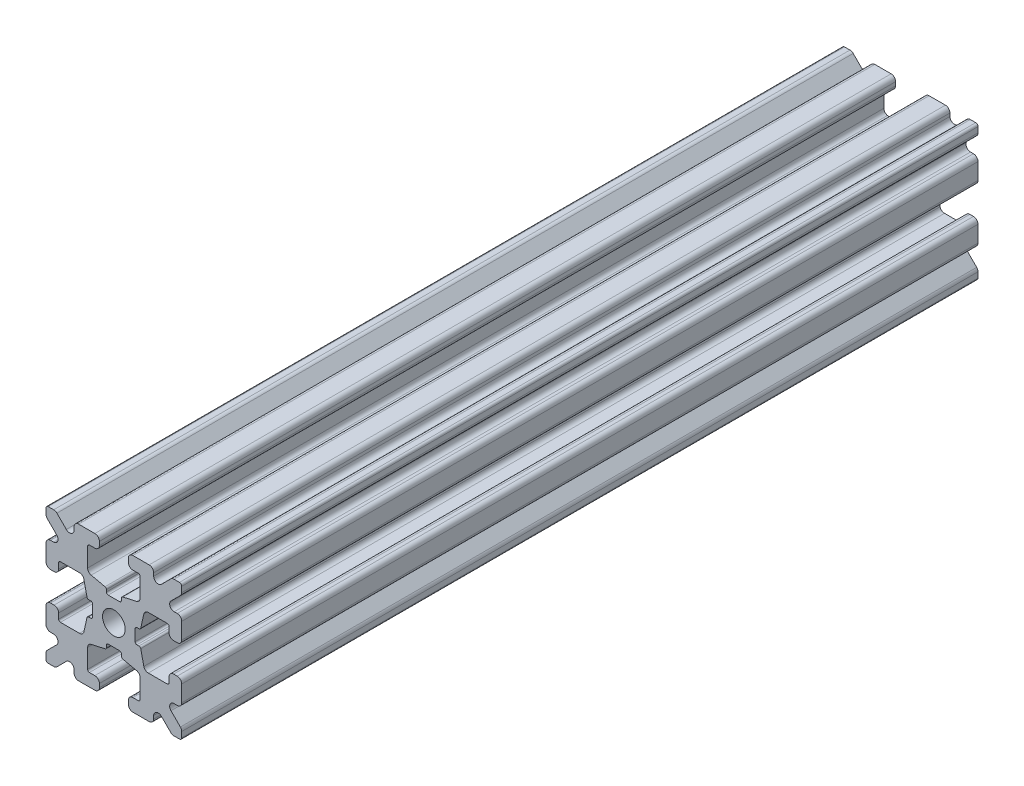
SolidWorks part; units mm, degrees
ref_plane "Front Plane" through (0, 0, 0) normal (0, 0, 1) x (1, 0, 0)
ref_plane "Top Plane" through (0, 0, 0) normal (0, 1, 0) x (1, 0, 0)
ref_plane "Right Plane" through (0, 0, 0) normal (1, 0, 0) x (0, 0, -1)
sketch "Sketch1" plane through (0, 0, 0) normal (0, 0, 1) x (1, 0, 0)
  line L1 (-7.5, -7.5) -> (7.5, -7.5)
  line L2 (-7.5, -7.5) -> (-7.5, 7.5)
  line L3 (-7.5, 7.5) -> (7.5, 7.5)
  line L4 (7.5, -7.5) -> (7.5, 7.5)
  line L5 (-7.5, -7.5) -> (7.5, 7.5) construction
  line L6 (-7.5, 7.5) -> (7.5, -7.5) construction
  circle A0 centre (0, 0) radius 1.25
  point P0 (0, 0)
  dimension "D2" = 2.5
  dimension "D1" = 15
extrude "Boss-Extrude1" add sketch "Sketch1" along normal mid plane 88
fillet "Fillet1" radius 0.25 4 edges at (7.5, -7.5, 0) (-7.5, -7.5, 0) (7.5, 7.5, 0) (-7.5, 7.5, 0)
sketch "Sketch2" plane through (0, 0, 44) normal (0, 0, 1) x (1, 0, 0)
  line L0 (-7.5, 7.25) -> (-7.5, -7.25) construction
  line L1 (-7.5, 1.6) -> (-6.1, 1.6)
  line L2 (-7.5, 1.6) -> (-7.5, -1.6)
  line L3 (-7.5, -1.6) -> (-6.1, -1.6)
  line L4 (-6.1, 1.6) -> (-6.1, 2.9)
  line L5 (0, 0) -> (-12.1036, 0) construction
  line L6 (-6.1, -2.9) -> (-3.4, -2.9)
  line L7 (0, 0) -> (-7.25, 7.25) construction
  line L8 (-6.1, 2.9) -> (-3.4, 2.9)
  line L9 (-3.4, -2.9) -> (-3.4, 2.9)
  line L10 (55, 0) -> (-55, 0) construction
  line L11 (-6.1, -2.9) -> (-6.1, -1.6)
  line L12 (2.9, 6.1) -> (1.6, 6.1)
  line L13 (2.9, 3.4) -> (-2.9, 3.4)
  line L14 (-2.9, 6.1) -> (-2.9, 3.4)
  line L15 (2.9, 6.1) -> (2.9, 3.4)
  line L16 (-1.6, 6.1) -> (-2.9, 6.1)
  line L17 (1.6, 7.5) -> (1.6, 6.1)
  line L18 (-1.6, 7.5) -> (1.6, 7.5)
  line L19 (-1.6, 7.5) -> (-1.6, 6.1)
  line L20 (-1.6, -7.5) -> (-1.6, -6.1)
  line L21 (-1.6, -7.5) -> (1.6, -7.5)
  line L22 (1.6, -7.5) -> (1.6, -6.1)
  line L23 (-1.6, -6.1) -> (-2.9, -6.1)
  line L24 (2.9, -6.1) -> (2.9, -3.4)
  line L25 (-2.9, -6.1) -> (-2.9, -3.4)
  line L26 (2.9, -3.4) -> (-2.9, -3.4)
  line L27 (2.9, -6.1) -> (1.6, -6.1)
  line L28 (6.1, -2.9) -> (6.1, -1.6)
  line L29 (3.4, -2.9) -> (3.4, 2.9)
  line L30 (6.1, 2.9) -> (3.4, 2.9)
  line L31 (6.1, -2.9) -> (3.4, -2.9)
  line L32 (6.1, 1.6) -> (6.1, 2.9)
  line L33 (7.5, -1.6) -> (6.1, -1.6)
  line L34 (7.5, 1.6) -> (7.5, -1.6)
  line L35 (7.5, 1.6) -> (6.1, 1.6)
  dimension "D1" = 3.2
  dimension "D2" = 5.8
  dimension "D3" = 1.4
  dimension "D4" = 2.7
extrude "Cut-Extrude1" cut sketch "Sketch2" against normal through all
sketch "Sketch4" plane through (0, 0, 44) normal (0, 0, 1) x (1, 0, 0)
  line L0 (-3.4, 2.9) -> (-2.75, 0)
  line L1 (55, 0) -> (-55, 0) construction
  line L2 (-2.75, 0) -> (-3.4, -2.9)
  line L3 (-3.4, -2.9) -> (-3.4, 2.9) construction
  line L4 (-3.4, 2.9) -> (-3.4, -2.9)
  line L5 (-2.9, 3.4) -> (0, 2.75)
  line L6 (0, 2.75) -> (2.9, 3.4)
  line L7 (2.9, 3.4) -> (-2.9, 3.4)
  line L8 (3.4, 2.9) -> (2.75, 0)
  line L9 (2.75, 0) -> (3.4, -2.9)
  line L10 (3.4, -2.9) -> (3.4, 2.9)
  line L11 (-2.9, -3.4) -> (0, -2.75)
  line L12 (0, -2.75) -> (2.9, -3.4)
  line L13 (2.9, -3.4) -> (-2.9, -3.4)
  circle A2 centre (0, 0) radius 2.75
  circle A3 centre (0, 0) radius 2.75 construction
  dimension "D1" = 1.5
extrude "Cut-Extrude3" cut sketch "Sketch4" against normal through all
fillet "Fillet3" radius 0.5 16 edges at (-6.1, -1.6, 0) (-7.5, -1.6, 0) (-6.1, 1.6, 0) (-7.5, 1.6, 0) (-1.6, -7.5, 0) (-1.6, -6.1, 0) (1.6, -7.5, 0) (1.6, -6.1, 0) (6.1, -1.6, 0) (7.5, -1.6, 0) (7.5, 1.6, 0) (6.1, 1.6, 0) (1.6, 7.5, 0) (1.6, 6.1, 0) (-1.6, 7.5, 0) (-1.6, 6.1, 0)
fillet "Fillet4" radius 0.5 8 edges at (-3.4, 2.9, 0) (-3.4, -2.9, 0) (2.9, -3.4, 0) (-2.9, -3.4, 0) (3.4, -2.9, 0) (3.4, 2.9, 0) (-2.9, 3.4, 0) (2.9, 3.4, 0)
fillet "Fillet5" radius 3 4 edges at (0, -2.75, 0) (2.75, 0, 0) (-2.75, 0, 0) (0, 2.75, 0)
fillet "Fillet6" radius 0.2 8 edges at (-2.9, -6.1, 0) (2.9, -6.1, 0) (6.1, -2.9, 0) (6.1, 2.9, 0) (2.9, 6.1, 0) (-2.9, 6.1, 0) (-6.1, -2.9, 0) (-6.1, 2.9, 0)
sketch "Sketch5" plane through (0, 0, 44) normal (0, 0, 1) x (1, 0, 0)
  line L0 (0, 0) -> (-7.25, 7.25) construction
  line L1 (-7.5, 6.4393) -> (-5.4607, 4.4)
  line L2 (-6.4393, 7.5) -> (-4.4, 5.4607)
  line L3 (-7.5, 4.4) -> (-5.4607, 4.4)
  line L4 (-3.8003, 2.9) -> (-5.9, 2.9) construction
  line L5 (0, 0) -> (-12.1819, 0) construction
  line L6 (-4.4, 7.5) -> (-4.4, 5.4607)
  line L7 (-2.9, 5.9) -> (-2.9, 3.8003) construction
  line L8 (-7.5, 6.4393) -> (-7.5, 4.4)
  line L9 (-7.5, 7.25) -> (-7.5, 2.1) construction
  line L10 (2.1, -7.5) -> (7.25, -7.5) construction
  line L11 (7.5, -7.25) -> (7.5, -2.1) construction
  line L12 (7.25, 7.5) -> (2.1, 7.5) construction
  line L13 (-2.1, 7.5) -> (-7.25, 7.5) construction
  line L14 (-4.4, 7.5) -> (-6.4393, 7.5)
  line L16 (55, 0) -> (-55, 0) construction
  line L17 (0, 0) -> (0, 10.993) construction
  line L18 (0, -54.6431) -> (0, 54.6431) construction
  line L20 (4.4, 7.5) -> (6.4393, 7.5)
  line L22 (7.5, 6.4393) -> (7.5, 4.4)
  line L23 (4.4, 7.5) -> (4.4, 5.4607)
  line L24 (7.5, 4.4) -> (5.4607, 4.4)
  line L25 (6.4393, 7.5) -> (4.4, 5.4607)
  line L26 (7.5, 6.4393) -> (5.4607, 4.4)
  line L27 (7.5, -6.4393) -> (5.4607, -4.4)
  line L28 (6.4393, -7.5) -> (4.4, -5.4607)
  line L29 (7.5, -4.4) -> (5.4607, -4.4)
  line L30 (4.4, -7.5) -> (4.4, -5.4607)
  line L31 (7.5, -6.4393) -> (7.5, -4.4)
  line L33 (4.4, -7.5) -> (6.4393, -7.5)
  line L36 (-4.4, -7.5) -> (-6.4393, -7.5)
  line L38 (-7.5, -6.4393) -> (-7.5, -4.4)
  line L39 (-4.4, -7.5) -> (-4.4, -5.4607)
  line L40 (-7.5, -4.4) -> (-5.4607, -4.4)
  line L41 (-6.4393, -7.5) -> (-4.4, -5.4607)
  line L42 (-7.5, -6.4393) -> (-5.4607, -4.4)
  dimension "D1" = 1.5
  dimension "D2" = 1.5
  dimension "D3" = 1.5
extrude "Cut-Extrude4" cut sketch "Sketch5" against normal through all
fillet "Fillet8" radius 0.5 24 edges at (-5.4607, 4.4, 0) (-7.5, 4.4, 0) (-5.4607, -4.4, 0) (-7.5, -4.4, 0) (-4.4, -7.5, 0) (-4.4, -5.4607, 0) (4.4, -7.5, 0) (4.4, -5.4607, 0) (5.4607, -4.4, 0) (7.5, -4.4, 0) (7.5, 4.4, 0) (5.4607, 4.4, 0) (4.4, 5.4607, 0) (4.4, 7.5, 0) (-4.4, 5.4607, 0) (-4.4, 7.5, 0) (-6.4393, 7.5, 0) (-7.5, 6.4393, 0) (6.4393, 7.5, 0) (7.5, 6.4393, 0) (6.4393, -7.5, 0) (7.5, -6.4393, 0) (-6.4393, -7.5, 0) (-7.5, -6.4393, 0)
sketch "Sketch6" plane through (0, 0, 44) normal (0, 0, 1) x (1, 0, 0)
  line L0 (0, 0) -> (0, 11.013) construction
  line L1 (0.6561, 2.8971) -> (2.1235, 2.8971) construction
  line L2 (0, -54.6431) -> (0, 54.6431) construction
  line L3 (0, 0) -> (7.25, 7.25) construction
  line L4 (7.5, 0.8255) -> (7.5, -0.8255)
  line L5 (2.3471, 0.8255) -> (7.5, 0.8255)
  line L6 (0, 0) -> (12.4016, 0) construction
  line L7 (0.8255, -7.5) -> (-0.8255, -7.5)
  line L8 (2.3471, -0.8255) -> (2.3471, 0.8255)
  line L9 (0.8255, -2.3471) -> (0.8255, -7.5)
  line L10 (7.5, -0.8255) -> (2.3471, -0.8255)
  line L11 (-7.5, -0.8255) -> (-2.3471, -0.8255)
  line L12 (-2.3471, -0.8255) -> (-2.3471, 0.8255)
  line L13 (-0.8255, -2.3471) -> (0.8255, -2.3471)
  line L14 (-0.8255, 7.5) -> (-0.8255, 2.3471)
  line L15 (-0.8255, 2.3471) -> (0.8255, 2.3471)
  line L16 (-0.8255, -7.5) -> (-0.8255, -2.3471)
  line L17 (0.8255, 2.3471) -> (0.8255, 7.5)
  line L18 (0.8255, 7.5) -> (-0.8255, 7.5)
  line L19 (3.9, 7.5) -> (2.1, 7.5) construction
  line L20 (-2.3471, 0.8255) -> (-7.5, 0.8255)
  line L21 (-7.5, 0.8255) -> (-7.5, -0.8255)
  point P5 (0, -2.5973)
  point P7 (0, 2.5973)
  dimension "D3" = 0.55
  dimension "D1" = 1.651
extrude "Cut-Extrude5" cut sketch "Sketch6" against normal through all
fillet "Fillet10" radius 0.2 16 edges at (-2.935, 0.8255, 0) (-2.935, -0.8255, 0) (2.935, -0.8255, 0) (2.935, 0.8255, 0) (0.8255, 2.935, 0) (-0.8255, 2.935, 0) (-2.3471, 0.8255, 0) (-2.3471, -0.8255, 0) (0.8255, 2.3471, 0) (-0.8255, 2.3471, 0) (2.3471, 0.8255, 0) (2.3471, -0.8255, 0) (0.8255, -2.935, 0) (0.8255, -2.3471, 0) (-0.8255, -2.3471, 0) (-0.8255, -2.935, 0)
